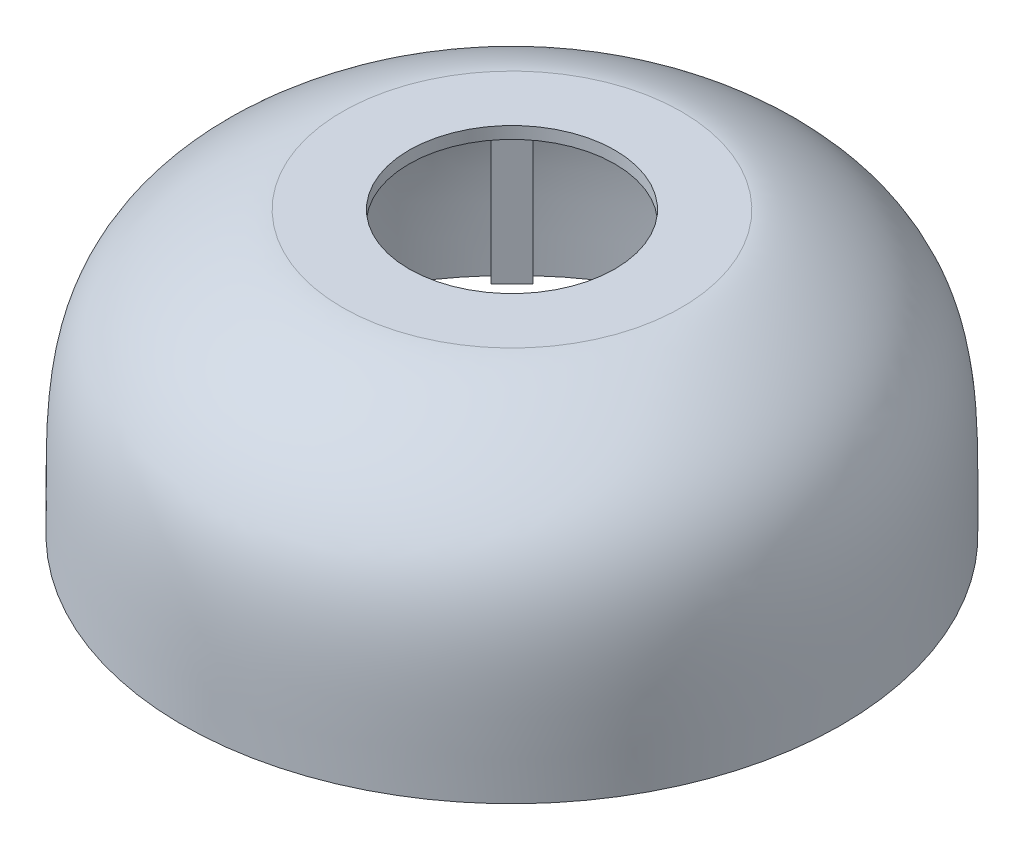
SolidWorks part; units mm, degrees
material "ABS"
ref_plane "Ebene vorne" through (0, 0, 0) normal (0, 0, 1) x (1, 0, 0)
ref_plane "Ebene oben" through (0, 0, 0) normal (0, 1, 0) x (1, 0, 0)
ref_plane "Ebene rechts" through (0, 0, 0) normal (1, 0, 0) x (0, 0, -1)
sketch "Skizze1" plane through (0, 0, 0) normal (0, 0, 1) x (1, 0, 0)
  line L0 (-55, 0) -> (55, 0) construction
  line L1 (40, 40) -> (-40, 40) construction
  line L2 (40, 0) -> (40, 40) construction
  line L3 (0, -12.151) -> (0, 47.849) construction
  line L4 (-40, 0) -> (-40, 40) construction
  line L6 (55, 0) -> (53, 0)
  line L7 (28.3108, 47) -> (17.1822, 47)
  line L8 (17.1822, 47) -> (17.1822, 45)
  line L9 (17.1822, 45) -> (28.3108, 45)
  spline S0 degree 3 poles (53, 0) (53.0483, 17.0063) (53.7497, 34.3408) (31.8155, 44.5551) (28.3108, 45) knots 0 0 0 0 0.631185 1 1 1 1
  spline S1 degree 3 poles (55, 0) (54.9364, 18.1626) (56.3964, 34.3686) (32.6894, 46.6851) (28.3108, 47) knots 0 0 0 0 0.647187 1 1 1 1
  point P10 (0, 40)
  point P12 (0, 0)
  dimension "D1" = 55
  dimension "D2" = 2
  dimension "D3" = 40
  dimension "D4" = 40
  dimension "D5" = 2
  dimension "D6" = 2
  dimension "D7" = 2
  dimension "D8" = 45
revolve "Rotation1" add sketch "Skizze1" angle 360 about L3
sketch "Skizze2" plane through (0, 0, 0) normal (0, -1, 0) x (1, 0, 0)
  line L0 (0, 0) -> (55, 0) construction
  line L1 (0, 0) -> (35.3553, 35.3553) construction
  line L2 (31.4663, 35.0018) -> (36.2132, 39.7487)
  line L3 (35.0018, 31.4663) -> (39.7487, 36.2132)
  line L4 (36.2132, 39.7487) -> (39.7487, 36.2132)
  line L5 (31.4663, 35.0018) -> (35.0018, 31.4663)
  line L6 (-31.4663, -35.0018) -> (-36.2132, -39.7487)
  line L7 (-35.0018, -31.4663) -> (-39.7487, -36.2132)
  line L8 (-36.2132, -39.7487) -> (-39.7487, -36.2132)
  line L9 (-31.4663, -35.0018) -> (-35.0018, -31.4663)
  line L10 (0, 0) -> (-35.3553, -35.3553) construction
  circle A0 centre (35.3553, 35.3553) radius 1.25
  circle A1 centre (0, 0) radius 55 construction
  circle A4 centre (-35.3553, -35.3553) radius 1.25
  point P20 (0, 0)
  point P24 (0, 0)
  dimension "D1" = 2.5
  dimension "D2" = 2.5
  dimension "D3" = 45
  dimension "D4" = 2.5
  dimension "D5" = 3
  dimension "D6" = 50
  dimension "D7" = 2
extrude "Aufsatz-Linear austragen3" add sketch "Skizze2" against normal up to surface (30.6997 mm away)
sketch "Skizze3" plane through (0, 0, 0) normal (0, -1, 0) x (1, 0, 0)
  circle A0 centre (0, 0) radius 53
extrude "Schnitt-Linear austragen1" cut sketch "Skizze3" against normal blind 3 contours A0
sketch "Skizze4" plane through (0, 0, 0) normal (1, 0, 0) x (0, 0, -1)
  line L0 (-55, 0) -> (55, 0) construction
  line L1 (-6.5, 0) -> (7.5, 0)
  line L2 (-6.5, 0) -> (-6.5, 11)
  line L3 (-6.5, 11) -> (7.5, 11)
  line L4 (7.5, 0) -> (7.5, 11)
  dimension "D1" = 14
  dimension "D2" = 11
  dimension "D3" = 6.5
extrude "Schnitt-Linear austragen2" cut sketch "Skizze4" against normal up to surface (54.6146 mm away)
